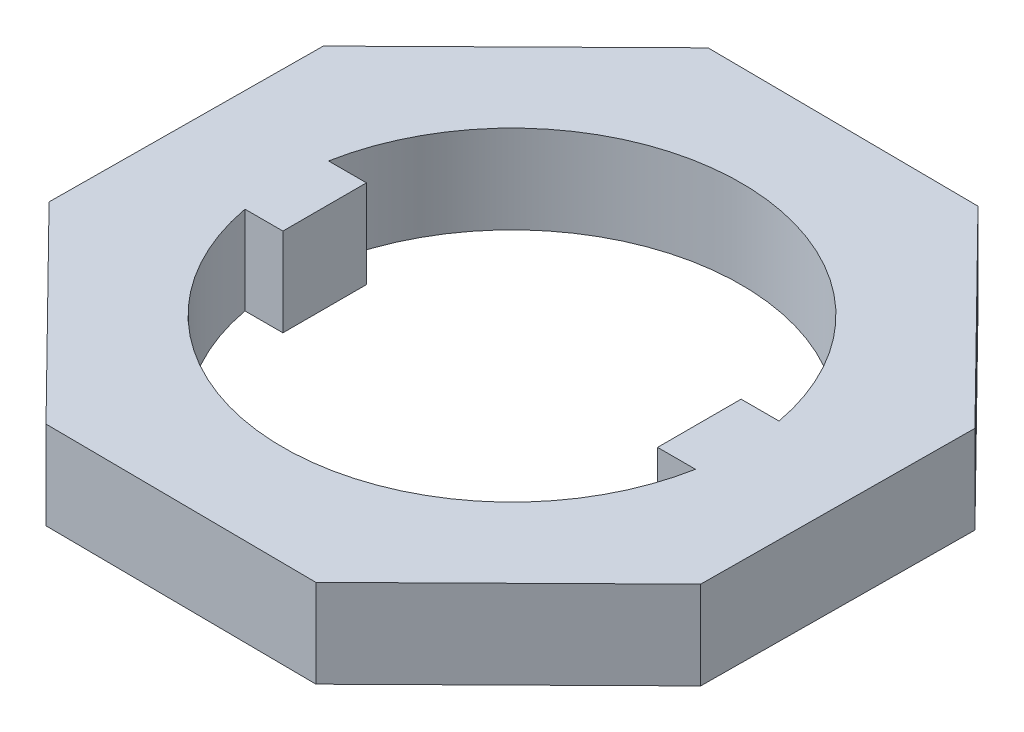
SolidWorks part; units mm, degrees
ref_plane "Front Plane" through (0, 0, 0) normal (0, 0, 1) x (1, 0, 0)
ref_plane "Top Plane" through (0, 0, 0) normal (0, 1, 0) x (1, 0, 0)
ref_plane "Right Plane" through (0, 0, 0) normal (1, 0, 0) x (0, 0, -1)
sketch "Sketch1" plane through (0, 0, 0) normal (0, 1, 0) x (1, 0, 0)
  line L0 (2.8752, -7.1015) -> (7.0546, -2.9884)
  line L1 (7.1015, 2.8752) -> (2.9884, 7.0546)
  line L2 (2.9884, 7.0546) -> (-2.8752, 7.1015)
  line L3 (-2.8752, 7.1015) -> (-7.0546, 2.9884)
  line L4 (-7.0546, 2.9884) -> (-7.1015, -2.8752)
  line L5 (-7.1015, -2.8752) -> (-2.9884, -7.0546)
  line L6 (-2.9884, -7.0546) -> (2.8752, -7.1015)
  line L7 (7.0546, -2.9884) -> (7.1015, 2.8752)
  line L9 (-4.8546, 0.9) -> (-4.0373, 0.9)
  line L10 (-4.0373, 0.9) -> (-4.0373, -0.9)
  line L11 (-4.0373, -0.9) -> (-4.8546, -0.9)
  line L13 (0, 0) -> (0, 50000) construction
  line L14 (4.0373, -0.9) -> (4.8546, -0.9)
  line L15 (4.8546, 0.9) -> (4.0373, 0.9)
  line L16 (4.0373, 0.9) -> (4.0373, -0.9)
  line L17 (0, 0) -> (-50000, 0) construction
  arc A0 (-4.8546, -0.9) -> (4.8546, -0.9) centre (0, 0) ccw
  circle A1 centre (0, 0) radius 7.0783 construction
  arc A2 (4.8546, 0.9) -> (-4.8546, 0.9) centre (0, 0) ccw
  dimension "D2" = 1.8
extrude "Boss-Extrude1" add sketch "Sketch1" along normal blind 1.9
